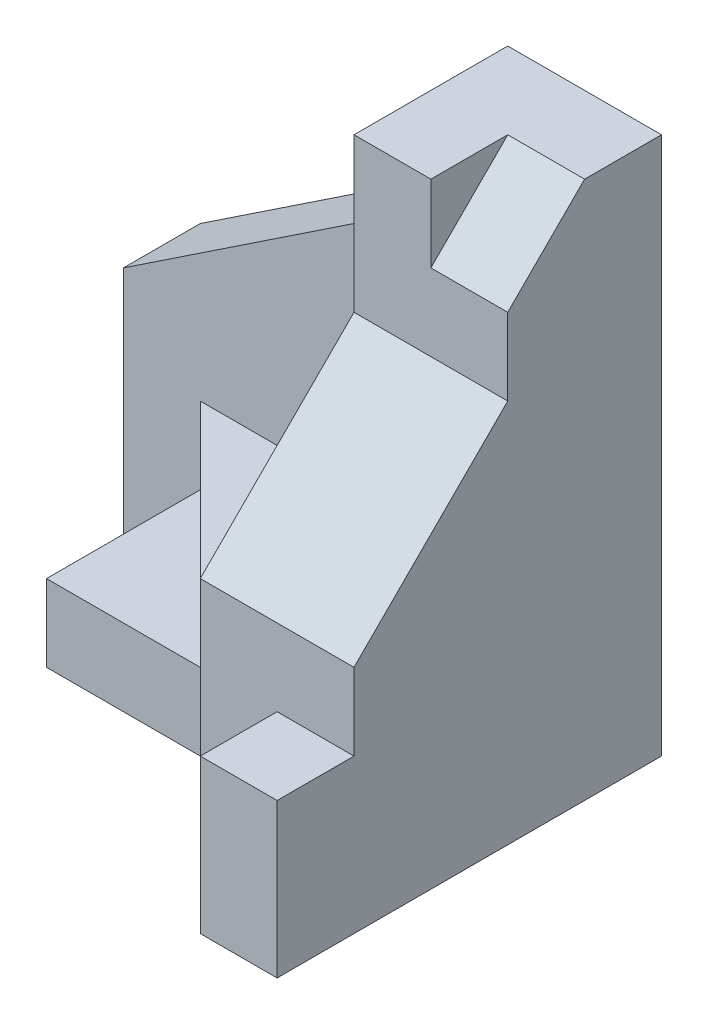
SolidWorks part; units mm, degrees
ref_plane "Front Plane" through (0, 0, 0) normal (0, 0, 1) x (1, 0, 0)
ref_plane "Top Plane" through (0, 0, 0) normal (0, 1, 0) x (1, 0, 0)
ref_plane "Right Plane" through (0, 0, 0) normal (1, 0, 0) x (0, 0, -1)
sketch "Sketch1" plane through (0, 0, 0) normal (0, 1, 0) x (1, 0, 0)
  line L0 (0, 0) -> (60, 0)
  line L1 (60, 0) -> (60, -50)
  line L2 (60, -50) -> (50, -50)
  line L3 (50, -50) -> (50, -40)
  line L4 (50, -40) -> (40, -40)
  line L5 (40, -40) -> (30, -30)
  line L6 (30, -30) -> (10, -30)
  line L7 (10, -30) -> (10, -10)
  line L8 (10, -10) -> (0, -10)
  line L9 (0, -10) -> (0, 0)
  dimension "D1" = 50
  dimension "D2" = 60
  dimension "D3" = 10
  dimension "D4" = 10
  dimension "D5" = 10
  dimension "D6" = 20
  dimension "D7" = 20
  dimension "D8" = 10
  dimension "D9" = 10
extrude "Boss-Extrude1" add sketch "Sketch1" along normal blind 20
sketch "Sketch2" plane through (0, 20, 0) normal (0, 1, 0) x (1, 0, 0)
  line L0 (30, -30) -> (10, -10)
  line L1 (10, -10) -> (10, -30)
  line L2 (10, -30) -> (30, -30)
extrude "Cut-Extrude1" cut sketch "Sketch2" against normal blind 10
sketch "Sketch3" plane through (0, 20, 0) normal (0, 1, 0) x (1, 0, 0)
  line L0 (0, 0) -> (60, 0)
  line L1 (60, -50) -> (60, 0) construction
  line L2 (40, -40) -> (60, -40)
  line L3 (60, -40) -> (60, 0)
  line L4 (40, -40) -> (40, -10)
  line L5 (10, -10) -> (0, -10)
  line L6 (0, -10) -> (0, 0)
  line L7 (40, -10) -> (10, -10)
extrude "Boss-Extrude2" add sketch "Sketch3" along normal blind 30
chamfer "Chamfer1" distance 20 1 edges at (50, 50, 40)
chamfer "Chamfer2" distance 20 distance2 30 1 edges at (0, 50, 5)
sketch "Sketch4" plane through (0, 50, 0) normal (0, 1, 0) x (1, 0, 0)
  line L1 (40, -20) -> (60, -20)
  line L2 (40, -20) -> (40, 0)
  line L3 (40, 0) -> (60, 0)
  line L4 (60, -20) -> (60, 0)
extrude "Boss-Extrude3" add sketch "Sketch4" along normal blind 20
sketch "Sketch5" plane through (60, 0, 0) normal (1, 0, 0) x (0, 0, -1)
  line L0 (-20, 70) -> (-10, 70)
  line L1 (-20, 70) -> (0, 70) construction
  line L2 (-10, 70) -> (-20, 60)
  line L3 (-20, 70) -> (-20, 50) construction
  line L4 (-20, 60) -> (-20, 70)
  dimension "D1" = 10
  dimension "D2" = 10
extrude "Cut-Extrude2" cut sketch "Sketch5" against normal blind 10
